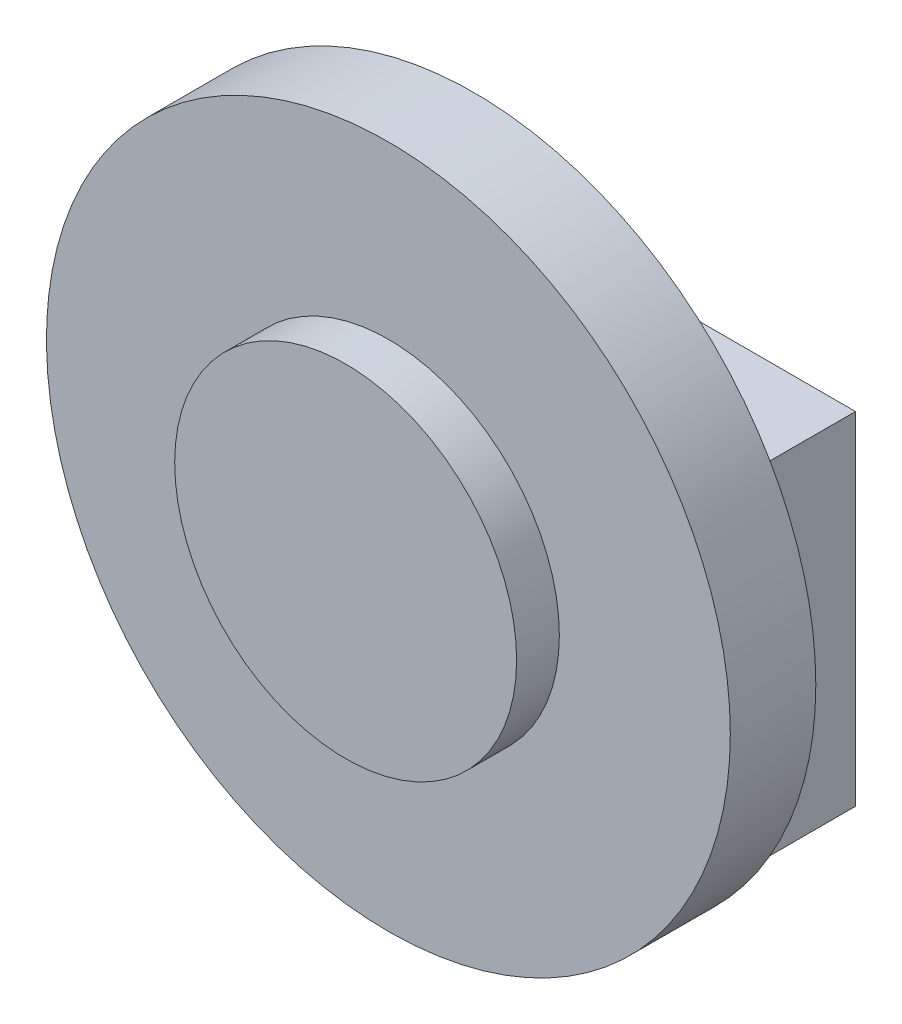
SolidWorks part; units mm, degrees
ref_plane "Plano frontal" through (0, 0, 0) normal (0, 0, 1) x (1, 0, 0)
ref_plane "Plano superior" through (0, 0, 0) normal (0, 1, 0) x (1, 0, 0)
ref_plane "Plano direito" through (0, 0, 0) normal (1, 0, 0) x (0, 0, -1)
sketch "Esboço1" plane through (0, 0, 0) normal (0, 0, 1) x (1, 0, 0)
  circle A0 centre (0, 0) radius 4
  dimension "D1" = 8
extrude "Ressalto-extrusão1" add sketch "Esboço1" along normal blind 1
sketch "Esboço2" plane through (0, 0, 1) normal (0, 0, 1) x (1, 0, 0)
  circle A0 centre (0, 0) radius 2
  dimension "D1" = 4
extrude "Ressalto-extrusão2" add sketch "Esboço2" along normal blind 0.5
sketch "Esboço3" plane through (0, 0, 0) normal (0, 0, -1) x (-1, 0, 0)
  line L1 (-3.4641, -2) -> (3.4641, -2)
  line L2 (-3.4641, -2) -> (-3.4641, 2)
  line L3 (-3.4641, 2) -> (3.4641, 2)
  line L4 (3.4641, -2) -> (3.4641, 2)
  line L5 (-3.4641, -2) -> (3.4641, 2) construction
  line L6 (-3.4641, 2) -> (3.4641, -2) construction
  circle A0 centre (0, 0) radius 4 construction
  point P0 (0, 0)
  dimension "D1" = 4
extrude "Ressalto-extrusão3" add sketch "Esboço3" along normal blind 1
